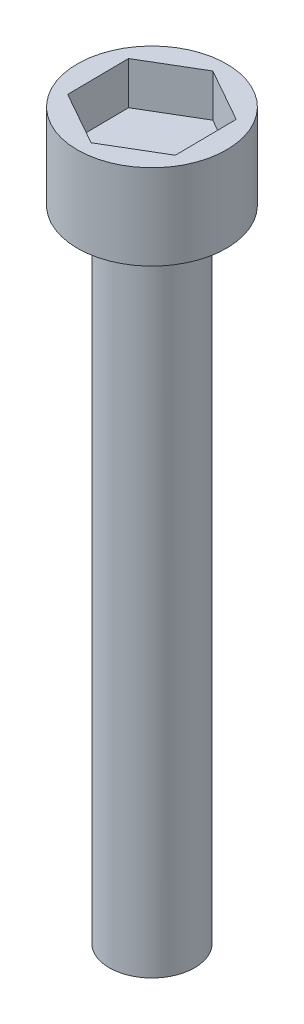
SolidWorks part; units mm, degrees
ref_plane "前视基准面" through (0, 0, 0) normal (0, 0, 1) x (1, 0, 0)
ref_plane "上视基准面" through (0, 0, 0) normal (0, 1, 0) x (1, 0, 0)
ref_plane "右视基准面" through (0, 0, 0) normal (1, 0, 0) x (0, 0, -1)
sketch "草图1" plane through (0, 0, 0) normal (0, 1, 0) x (1, 0, 0)
  circle A0 centre (0, 0) radius 3.5
  dimension "D1" = 7
extrude "凸台-拉伸1" add sketch "草图1" against normal blind 4 contours A0
sketch "草图2" plane through (0, -4, 0) normal (0, -1, 0) x (1, 0, 0)
  circle A0 centre (0, 0) radius 2
  dimension "D1" = 4
extrude "凸台-拉伸2" add sketch "草图2" along normal blind 30
sketch "草图3" plane through (0, 0, 0) normal (0, 1, 0) x (1, 0, 0)
  line L1 (2.5156, -1.4161) -> (2.4842, 1.4705)
  line L2 (2.4842, 1.4705) -> (-0.0314, 2.8866)
  line L3 (-0.0314, 2.8866) -> (-2.5156, 1.4161)
  line L4 (-2.5156, 1.4161) -> (-2.4842, -1.4705)
  line L5 (-2.4842, -1.4705) -> (0.0314, -2.8866)
  line L6 (0.0314, -2.8866) -> (2.5156, -1.4161)
  circle A0 centre (0, 0) radius 2.5 construction
  dimension "D1" = 5
extrude "切除-拉伸1" cut sketch "草图3" against normal blind 2 contours L2 L3 L4 L5 L6 L1
